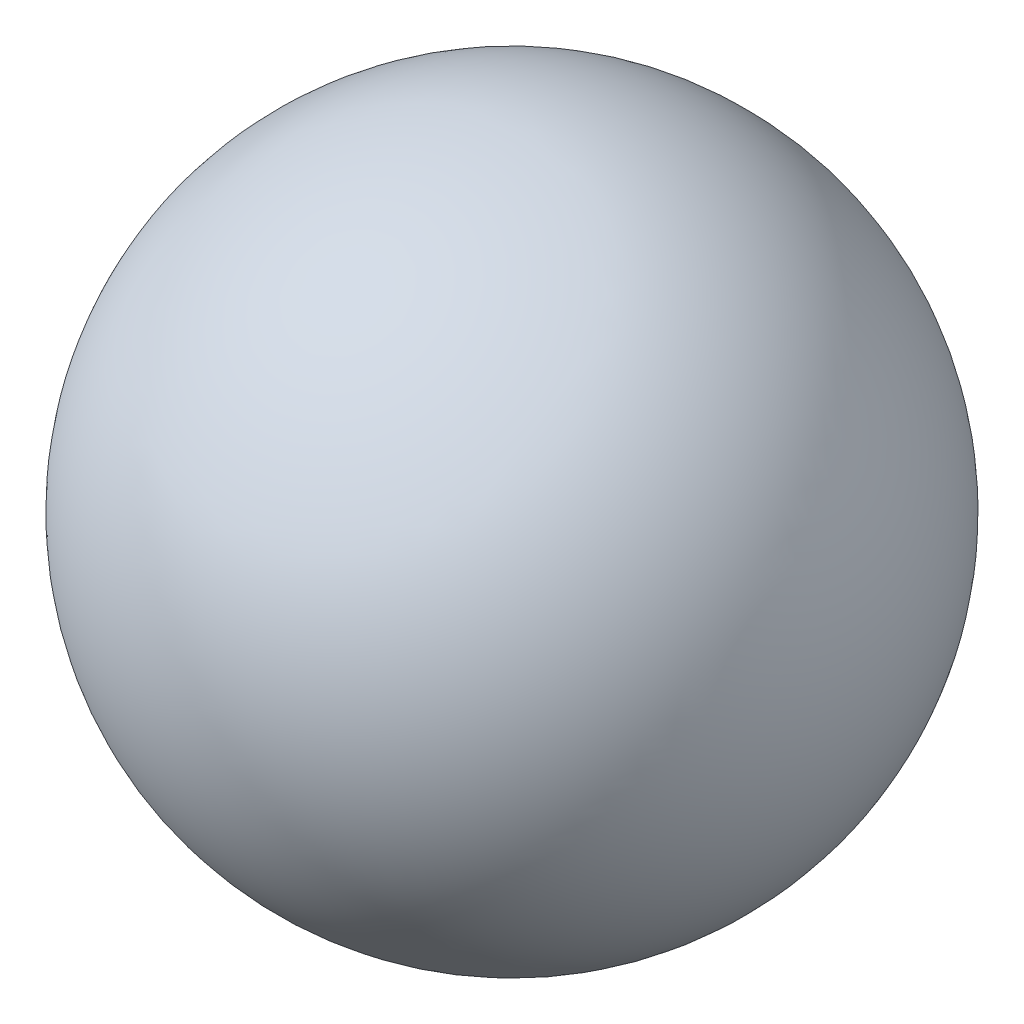
SolidWorks part; units mm, degrees
material "Natural Rubber"
ref_plane "Front" through (0, 0, 0) normal (0, 0, 1) x (1, 0, 0)
ref_plane "Top" through (0, 0, 0) normal (0, 1, 0) x (1, 0, 0)
ref_plane "Right" through (0, 0, 0) normal (1, 0, 0) x (0, 0, -1)
sketch "Sketch1" plane through (0, 0, 0) normal (0, 0, 1) x (1, 0, 0)
  line L0 (-54.7601, 0) -> (64.2066, 0) construction
  line L1 (0, 44.2066) -> (0, -51.5867) construction
  line L2 (0, 0) -> (0, 19)
  line L3 (0, 0) -> (19, 0)
  arc A0 (0, 19) -> (19, 0) centre (0, 0) cw
  dimension "D2" = 19
  dimension "D1" = 38
revolve "Revolve2" add sketch "Sketch1" angle 360 about L0
mirror "Mirror1" about plane through (0, 0, 0) normal (1, 0, 0) of "Revolve2"
